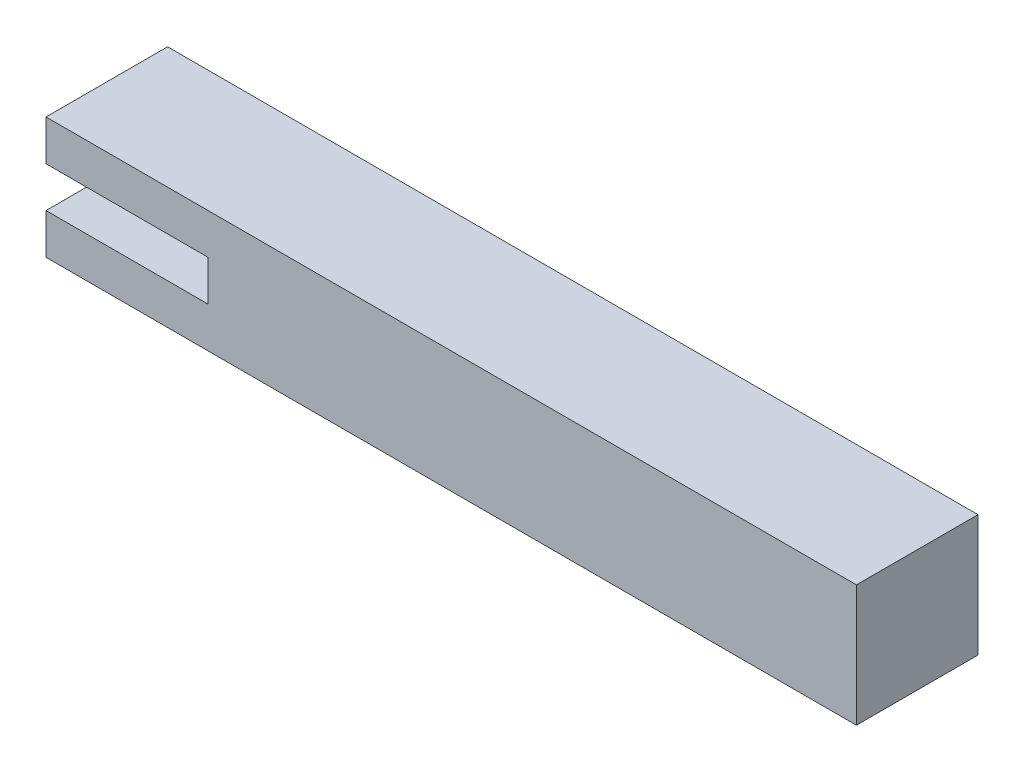
SolidWorks part; units mm, degrees
material "Cast Stainless Steel"
ref_plane "Front Plane" through (0, 0, 0) normal (0, 0, 1) x (1, 0, 0)
ref_plane "Top Plane" through (0, 0, 0) normal (0, 1, 0) x (1, 0, 0)
ref_plane "Right Plane" through (0, 0, 0) normal (1, 0, 0) x (0, 0, -1)
sketch "Sketch2" plane through (0, 0, 0) normal (1, 0, 0) x (0, 0, -1)
  line L1 (0, 0) -> (30, 0)
  line L2 (0, 0) -> (0, 30)
  line L3 (0, 30) -> (30, 30)
  line L4 (30, 0) -> (30, 30)
  dimension "D1" = 30
  dimension "D2" = 30
extrude "Boss-Extrude1" add sketch "Sketch2" along normal blind 200
sketch "Sketch3" plane through (0, 0, 0) normal (0, 0, 1) x (1, 0, 0)
  line L0 (0, 10) -> (40, 10)
  line L2 (0, 20) -> (40, 20)
  line L3 (0, 10) -> (0, 20)
  line L4 (40, 20) -> (40, 10)
  dimension "D1" = 10
extrude "Cut-Extrude1" cut sketch "Sketch3" against normal blind 10
